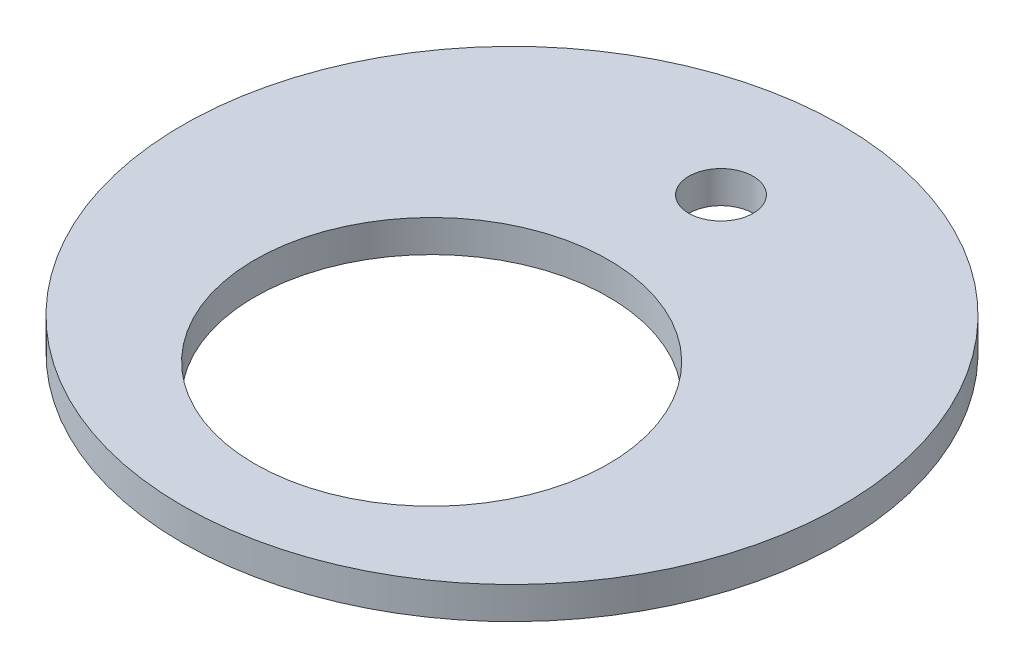
SolidWorks part; units mm, degrees
material "AISI 304"
ref_plane "Front Plane" through (0, 0, 0) normal (0, 0, 1) x (1, 0, 0)
ref_plane "Top Plane" through (0, 0, 0) normal (0, 1, 0) x (1, 0, 0)
ref_plane "Right Plane" through (0, 0, 0) normal (1, 0, 0) x (0, 0, -1)
sketch "Sketch1" plane through (0, 0, 0) normal (0, 1, 0) x (1, 0, 0)
  line L0 (0, 0) -> (0, -5)
  line L1 (0, 0) -> (0, 13)
  circle A0 centre (0, 0) radius 20.5
  circle A1 centre (0, -5) radius 11
  circle A2 centre (0, 13) radius 2
  dimension "D1" = 13
  dimension "D3" = 22
  dimension "D4" = 41
  dimension "D2" = 5
extrude "Boss-Extrude1" add sketch "Sketch1" along normal blind 2
